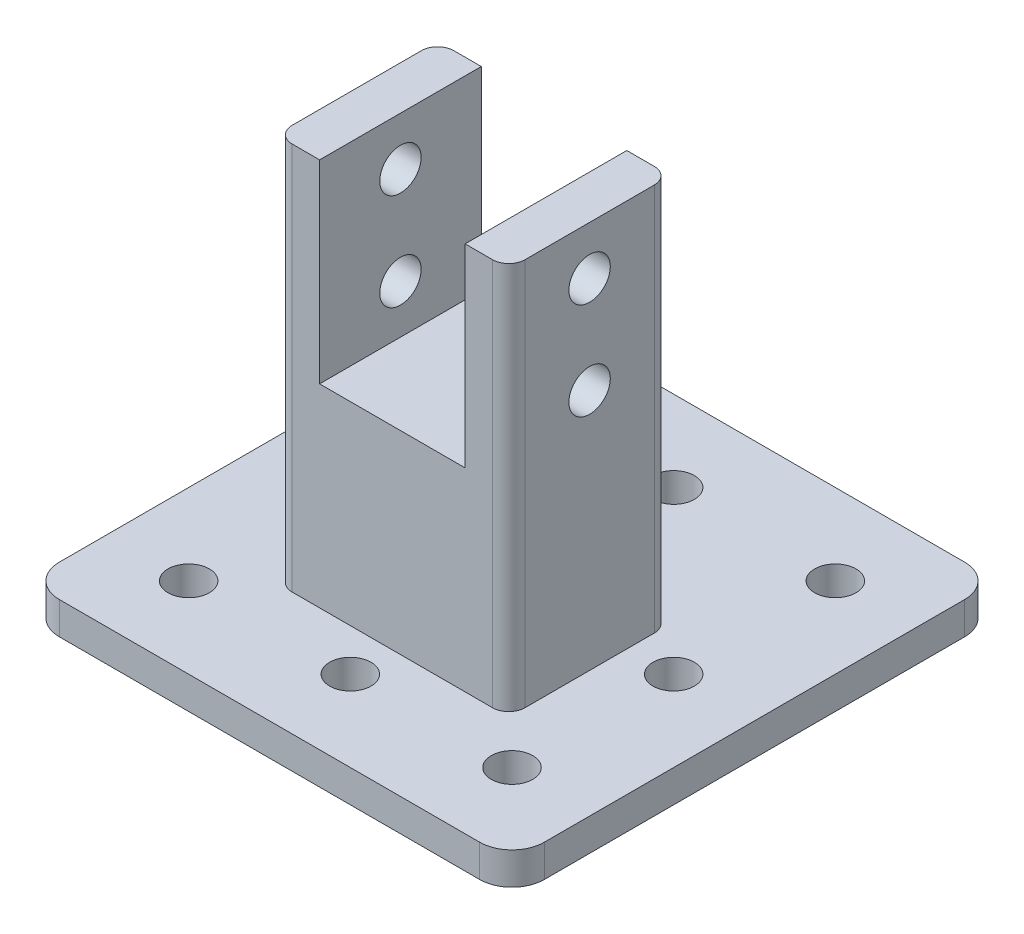
SolidWorks part; units mm, degrees
ref_plane "정면" through (0, 0, 0) normal (0, 0, 1) x (1, 0, 0)
ref_plane "윗면" through (0, 0, 0) normal (0, 1, 0) x (1, 0, 0)
ref_plane "우측면" through (0, 0, 0) normal (1, 0, 0) x (0, 0, -1)
sketch "스케치1" plane through (0, 0, 0) normal (0, 1, 0) x (1, 0, 0)
  line L1 (-32.5, 37.5) -> (32.5, 37.5)
  line L2 (-37.5, 32.5) -> (-37.5, -32.5)
  line L3 (-32.5, -37.5) -> (32.5, -37.5)
  line L4 (37.5, 32.5) -> (37.5, -32.5)
  arc A0 (-37.5, -32.5) -> (-32.5, -37.5) centre (-32.5, -32.5) ccw
  arc A1 (32.5, -37.5) -> (37.5, -32.5) centre (32.5, -32.5) ccw
  arc A2 (32.5, 37.5) -> (37.5, 32.5) centre (32.5, 32.5) cw
  arc A3 (-32.5, 37.5) -> (-37.5, 32.5) centre (-32.5, 32.5) ccw
  point P8 (37.5, -37.5)
  point P11 (37.5, 37.5)
  point P14 (0, 37.5)
  point P16 (37.5, 0)
  dimension "D3" = 5
  dimension "D1" = 75
  dimension "D2" = 75
extrude "보스-돌출2" add sketch "스케치1" along normal blind 5
sketch "스케치2" plane through (0, 5, 0) normal (0, 1, 0) x (1, 0, 0)
  line L0 (0, -2.75) -> (0, 2.75) construction
  circle A0 centre (0, 25) radius 3.2
  circle A1 centre (-25, 25) radius 3.2
  circle A2 centre (-25, 0) radius 3.2
  circle A3 centre (-25, -25) radius 3.2
  circle A4 centre (0, -25) radius 3.2
  circle A5 centre (25, -25) radius 3.2
  circle A6 centre (25, 0) radius 3.2
  circle A7 centre (25, 25) radius 3.2
  point P19 (0, 0)
  point P20 (0, 0)
  point P21 (0, 0)
  point P22 (0, 0)
  point P23 (0, 0)
  point P24 (0, 0)
  dimension "D1" = 6.4
  dimension "D2" = 25
  dimension "D3" = 25
  dimension "D4" = 25
  dimension "D5" = 25
extrude "컷-돌출1" cut sketch "스케치2" against normal up to surface (5 mm away) up to face at (0, 0, 0)
ref_plane "평면1" through (0, 35, 0) normal (0, -1, 0) x (-1, 0, 0)
sketch "스케치4" plane through (0, 35, 0) normal (0, -1, 0) x (-1, 0, 0)
  line L1 (-18, 6.5) -> (18, 6.5)
  line L2 (-18, 6.5) -> (-18, -18.5)
  line L3 (-18, -18.5) -> (18, -18.5)
  line L4 (18, 6.5) -> (18, -18.5)
  point P4 (0, -18.5)
  point P6 (-18, -6)
  dimension "D3" = 6
  dimension "D1" = 36
  dimension "D2" = 25
extrude "보스-돌출3" add sketch "스케치4" along normal up to surface (30 mm away) up to face at (-25, 5, -21.8)
fillet "필렛1" radius 2.5 4 edges at (-18, 20, 18.5) (-18, 20, -6.5) (18, 20, -6.5) (18, 20, 18.5)
ref_plane "평면2" through (0, 65, 0) normal (0, -1, 0) x (-1, 0, 0)
sketch "스케치5" plane through (0, 65, 0) normal (0, -1, 0) x (-1, 0, 0)
  line L0 (18, -16) -> (18, 4) construction
  line L1 (15.5, -18.5) -> (-15.5, -18.5) construction
  line L2 (-18, -16) -> (-18, 4) construction
  line L3 (-15.5, 6.5) -> (15.5, 6.5) construction
  line L4 (18, -16) -> (18, 4)
  line L5 (15.5, -18.5) -> (11.25, -18.5)
  line L6 (-18, -16) -> (-18, 4)
  line L7 (-15.5, 6.5) -> (-11.25, 6.5)
  line L8 (11.25, 6.5) -> (15.5, 6.5)
  line L9 (-11.25, -18.5) -> (-15.5, -18.5)
  line L10 (-11.25, 6.5) -> (-11.25, -18.5)
  line L12 (11.25, 6.5) -> (11.25, -18.5)
  arc A0 (18, 4) -> (15.5, 6.5) centre (15.5, 4) ccw construction
  arc A1 (15.5, -18.5) -> (18, -16) centre (15.5, -16) ccw construction
  arc A2 (-18, -16) -> (-15.5, -18.5) centre (-15.5, -16) ccw construction
  arc A3 (-15.5, 6.5) -> (-18, 4) centre (-15.5, 4) ccw construction
  arc A4 (18, 4) -> (15.5, 6.5) centre (15.5, 4) ccw
  arc A5 (15.5, -18.5) -> (18, -16) centre (15.5, -16) ccw
  arc A6 (-18, -16) -> (-15.5, -18.5) centre (-15.5, -16) ccw
  arc A7 (-15.5, 6.5) -> (-18, 4) centre (-15.5, 4) ccw
  dimension "D1" = 22.5
  dimension "D2" = 11.25
extrude "보스-돌출4" add sketch "스케치5" along normal up to surface (30 mm away) up to face at (0, 35, 6)
sketch "스케치6" plane through (18, 0, 0) normal (1, 0, 0) x (0, 0, -1)
  line L1 (-41.25, 65) -> (41.25, 65) construction
  line L4 (-18.5, 5) -> (-18.5, 65) construction
  circle A0 centre (-6, 57.5) radius 3.2
  circle A1 centre (-6, 42.5) radius 3.2
  point P6 (0, 0)
  point P7 (0, 0)
  point P10 (0, 0)
  dimension "D1" = 6.4
  dimension "D2" = 15
  dimension "D3" = 7.5
  dimension "D4" = 12.5
extrude "컷-돌출2" cut sketch "스케치6" against normal up to surface (36 mm away) up to face at (-18, 35, 6)
